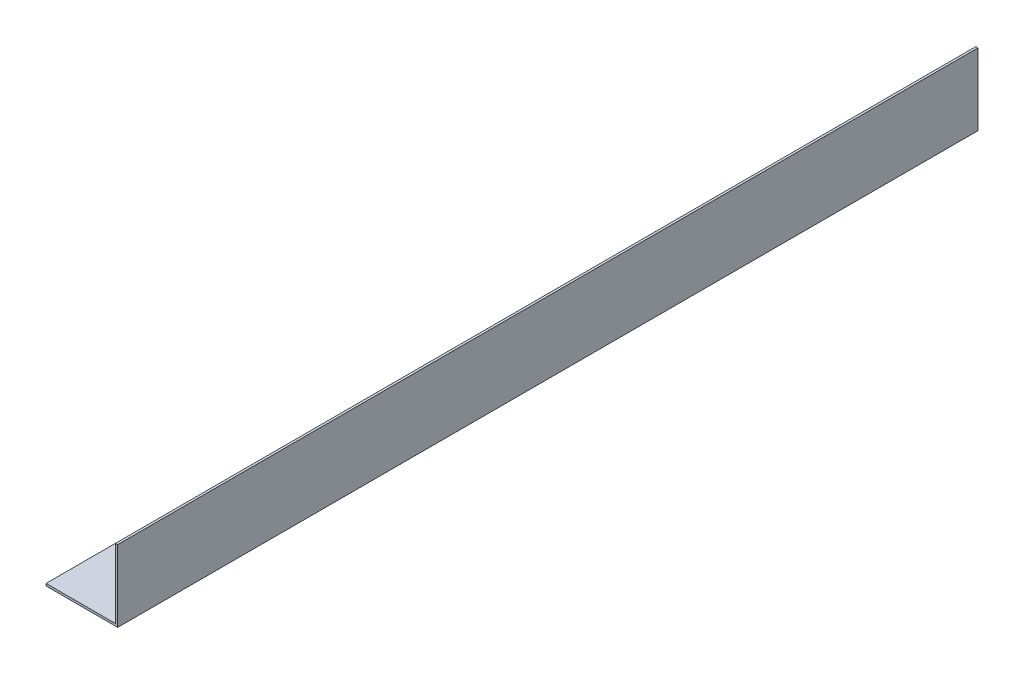
SolidWorks part; units mm, degrees
ref_plane "Front Plane" through (0, 0, 0) normal (0, 0, 1) x (1, 0, 0)
ref_plane "Top Plane" through (0, 0, 0) normal (0, 1, 0) x (1, 0, 0)
ref_plane "Right Plane" through (0, 0, 0) normal (1, 0, 0) x (0, 0, -1)
sketch "Sketch1" plane through (0, 0, 0) normal (0, 0, 1) x (1, 0, 0)
  line L0 (0, 0) -> (50.8, 0)
  line L1 (50.8, 0) -> (50.8, 50.8)
  line L2 (50.8, 50.8) -> (49.2125, 50.8)
  line L3 (49.2125, 50.8) -> (49.2125, 1.5875)
  line L4 (49.2125, 1.5875) -> (0, 1.5875)
  line L5 (0, 1.5875) -> (0, 0)
  dimension "D1" = 50.8
  dimension "D2" = 50.8
  dimension "D3" = 1.5875
  dimension "D4" = 1.5875
extrude "Extrude1" add sketch "Sketch1" along normal blind 609.6
sketch "Sketch2" plane through (0, 0, 0) normal (0, -1, 0) x (1, 0, 0)
  line L0 (20.6375, 556.5521) -> (36.7072, 556.5521)
  line L1 (0, 609.6) -> (50.8, 609.6) construction
  line L2 (36.7072, 61.2521) -> (20.6375, 61.2521)
  line L3 (0, 304.8) -> (50.8, 304.8) construction
  line L4 (0, 609.6) -> (0, 0) construction
  line L5 (50.8, 609.6) -> (50.8, 0) construction
  line L6 (36.7072, 548.3479) -> (20.6375, 548.3479)
  line L7 (20.6375, 53.0479) -> (36.7072, 53.0479)
  arc A0 (20.6375, 556.5521) -> (20.6375, 548.3479) centre (20.6375, 552.45) ccw
  arc A1 (36.7072, 61.2521) -> (36.7072, 53.0479) centre (36.7072, 57.15) cw
  arc A2 (36.7072, 548.3479) -> (36.7072, 556.5521) centre (36.7072, 552.45) ccw
  arc A3 (20.6375, 53.0479) -> (20.6375, 61.2521) centre (20.6375, 57.15) cw
  dimension "D1" = 8.2042
  dimension "D2" = 57.15
  dimension "D3" = 20.6375
extrude "Cut-Extrude1" cut sketch "Sketch2" against normal through all
